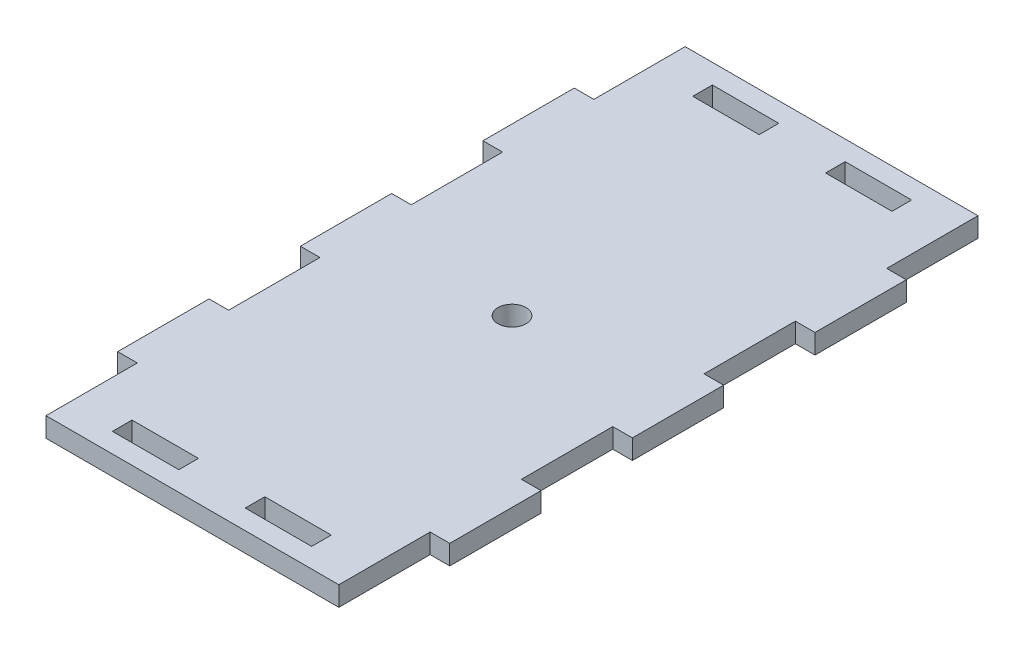
SolidWorks part; units mm, degrees
ref_plane "Front Plane" through (0, 0, 0) normal (0, 0, 1) x (1, 0, 0)
ref_plane "Top Plane" through (0, 0, 0) normal (0, 1, 0) x (1, 0, 0)
ref_plane "Right Plane" through (0, 0, 0) normal (1, 0, 0) x (0, 0, -1)
sketch "Sketch1" plane through (0, 0, 0) normal (0, 1, 0) x (1, 0, 0)
  line L1 (0, 0) -> (50.8, 0)
  line L2 (0, 0) -> (0, 97.79)
  line L3 (0, 97.79) -> (50.8, 97.79)
  line L4 (50.8, 0) -> (50.8, 97.79)
  dimension "D1" = 50.8
  dimension "D2" = 97.79
extrude "Boss-Extrude1" add sketch "Sketch1" along normal blind 3
sketch "Sketch2" plane through (0, 3, 0) normal (0, 1, 0) x (1, 0, 0)
  line L0 (50.8, 97.79) -> (0, 97.79) construction
  line L1 (10.16, 94.79) -> (20.32, 94.79)
  line L2 (10.16, 94.79) -> (10.16, 91.79)
  line L3 (10.16, 91.79) -> (20.32, 91.79)
  line L4 (20.32, 94.79) -> (20.32, 91.79)
  line L5 (30.48, 94.79) -> (40.64, 94.79)
  line L6 (30.48, 94.79) -> (30.48, 91.79)
  line L7 (30.48, 91.79) -> (40.64, 91.79)
  line L8 (40.64, 94.79) -> (40.64, 91.79)
  line L9 (47.8, 97.79) -> (50.8, 97.79)
  line L10 (47.8, 97.79) -> (47.8, 83.82)
  line L11 (47.8, 83.82) -> (50.8, 83.82)
  line L12 (50.8, 97.79) -> (50.8, 83.82)
  line L13 (50.8, 0) -> (50.8, 97.79) construction
  line L14 (47.8, 83.82) -> (47.8, 69.85) construction
  line L15 (47.8, 69.85) -> (50.8, 69.85)
  line L16 (47.8, 69.85) -> (47.8, 55.88)
  line L17 (47.8, 55.88) -> (50.8, 55.88)
  line L18 (50.8, 69.85) -> (50.8, 55.88)
  line L19 (47.8, 41.91) -> (50.8, 41.91)
  line L20 (47.8, 41.91) -> (47.8, 27.94)
  line L21 (47.8, 27.94) -> (50.8, 27.94)
  line L22 (50.8, 41.91) -> (50.8, 27.94)
  line L23 (47.8, 13.97) -> (50.8, 13.97)
  line L24 (47.8, 13.97) -> (47.8, 0)
  line L25 (47.8, 0) -> (50.8, 0)
  line L26 (50.8, 13.97) -> (50.8, 0)
  line L27 (47.8, 69.85) -> (66.85, 69.7233) construction
  line L28 (47.8, 55.88) -> (47.8, 41.91) construction
  line L29 (47.8, 27.94) -> (47.8, 13.97) construction
  line L30 (40.64, 91.79) -> (50.8, 91.79) construction
  line L31 (30.48, 91.79) -> (20.32, 91.79) construction
  line L32 (10.16, 91.79) -> (0, 91.79) construction
  line L33 (0, 97.79) -> (0, 0) construction
  line L34 (25.4, 97.79) -> (25.4, 0) construction
  line L35 (0, 0) -> (50.8, 0) construction
  line L36 (0, 48.895) -> (50.8, 48.895) construction
  line L37 (40.64, 3) -> (40.64, 6)
  line L38 (30.48, 6) -> (40.64, 6)
  line L39 (30.48, 3) -> (40.64, 3)
  line L40 (30.48, 3) -> (30.48, 6)
  line L41 (20.32, 3) -> (20.32, 6)
  line L42 (10.16, 6) -> (20.32, 6)
  line L43 (10.16, 3) -> (20.32, 3)
  line L44 (10.16, 3) -> (10.16, 6)
  line L45 (3, 0) -> (0, 0)
  line L46 (0, 13.97) -> (0, 0)
  line L47 (3, 13.97) -> (3, 0)
  line L48 (3, 13.97) -> (0, 13.97)
  line L49 (3, 27.94) -> (0, 27.94)
  line L50 (0, 41.91) -> (0, 27.94)
  line L51 (3, 41.91) -> (3, 27.94)
  line L52 (3, 41.91) -> (0, 41.91)
  line L53 (3, 55.88) -> (0, 55.88)
  line L54 (0, 69.85) -> (0, 55.88)
  line L55 (3, 69.85) -> (3, 55.88)
  line L56 (3, 69.85) -> (0, 69.85)
  line L57 (3, 97.79) -> (0, 97.79)
  line L58 (0, 97.79) -> (0, 83.82)
  line L59 (3, 83.82) -> (0, 83.82)
  line L60 (3, 97.79) -> (3, 83.82)
  dimension "D1" = 3
  dimension "D2" = 3
  dimension "D3" = 3
  dimension "D4" = 3
extrude "Cut-Extrude1" cut sketch "Sketch2" against normal through all
hole_wizard "#8 Clearance Hole2" positions "Sketch5" profile "Sketch4" hole size "#8" standard "ANSI Inch" end condition through all
sketch "Sketch5" plane through (0, 3, 0) normal (0, 1, 0) x (1, 0, 0)
  line L2 (3, 97.79) -> (3, 0) construction
  line L4 (47.8, 97.79) -> (47.8, 0) construction
  line L6 (25.4, 48.895) -> (3, 48.895) construction
  line L8 (25.4, 48.895) -> (47.8, 48.895) construction
  line L9 (25.4, 97.79) -> (25.4, 48.895) construction
  line L10 (47.8, 97.79) -> (3, 97.79) construction
  line L11 (25.4, 48.895) -> (25.4, 0) construction
  line L12 (3, 0) -> (47.8, 0) construction
  point P0 (25.4, 48.895)
sketch "Sketch4" plane through (25.4, 3, -48.895) normal (1, 0, 0) x (0, 0, 1)
  line L0 (0, 0) -> (0, 3)
  line L1 (0, 3) -> (2.1526, 3)
  line L2 (2.1526, 3) -> (2.1526, 0)
  line L5 (2.1526, 0) -> (0, 0)
  line L11 (0, -6.35) -> (0, 107.95) construction
  dimension "Thru Hole Dia." = 4.3053
  dimension "Thru Hole Depth" = 3
